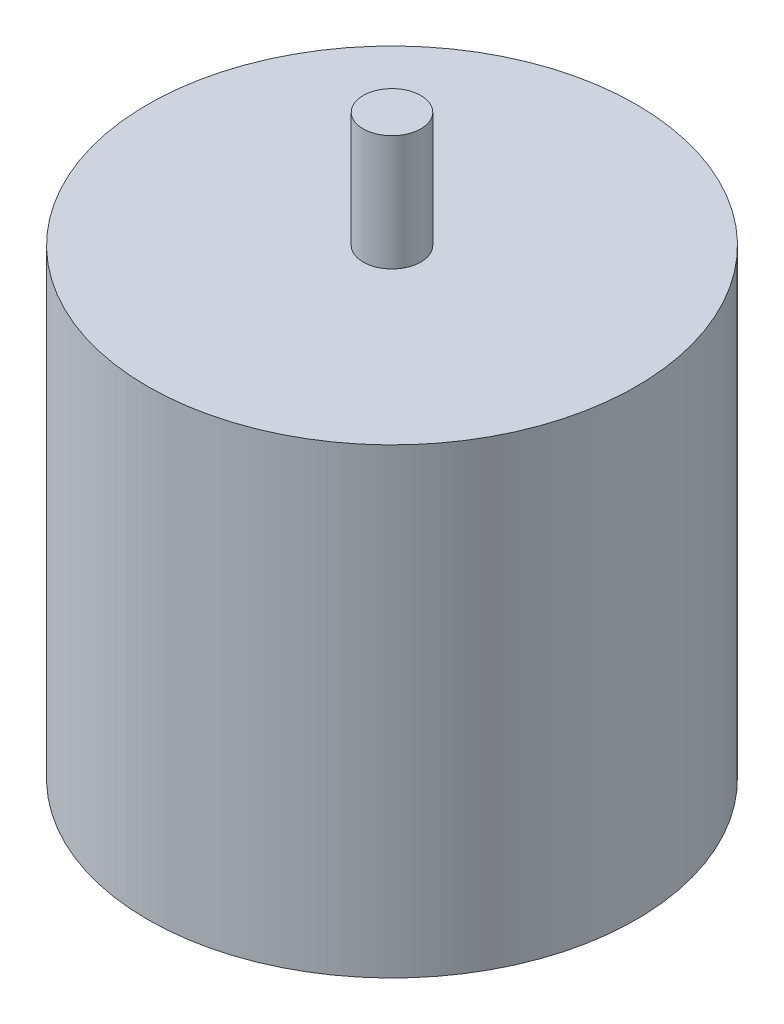
SolidWorks part; units mm, degrees
ref_plane "Front Plane" through (0, 0, 0) normal (0, 0, 1) x (1, 0, 0)
ref_plane "Top Plane" through (0, 0, 0) normal (0, 1, 0) x (1, 0, 0)
ref_plane "Right Plane" through (0, 0, 0) normal (1, 0, 0) x (0, 0, -1)
sketch "Sketch1" plane through (0, 0, 0) normal (0, 1, 0) x (1, 0, 0)
  circle A0 centre (0, 0) radius 21.1667
  circle A1 centre (0, 0) radius 2.5
  dimension "D1" = 42.3333
  dimension "D2" = 5
extrude "Boss-Extrude1" add sketch "Sketch1" along normal blind 40
sketch "Sketch2" plane through (0, 40, 0) normal (0, 1, 0) x (1, 0, 0)
  circle A0 centre (0, 0) radius 2.5
  dimension "D1" = 5
extrude "Boss-Extrude2" add sketch "Sketch2" along normal blind 10 and the other way blind 30
